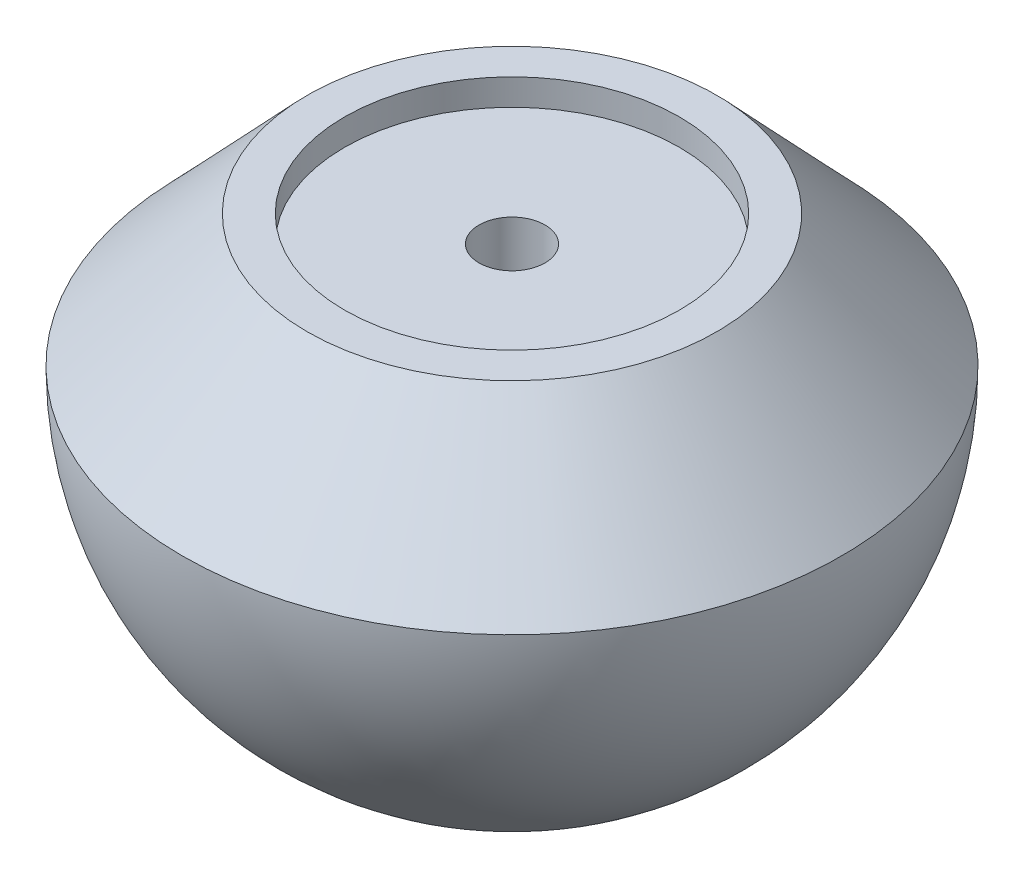
SolidWorks part; units mm, degrees
ref_plane "Front Plane" through (0, 0, 0) normal (0, 0, 1) x (1, 0, 0)
ref_plane "Top Plane" through (0, 0, 0) normal (0, 1, 0) x (1, 0, 0)
ref_plane "Right Plane" through (0, 0, 0) normal (1, 0, 0) x (0, 0, -1)
other "Configuration Table"
sketch "Sketch1" plane through (0, 0, 0) normal (0, 0, 1) x (1, 0, 0)
  line L0 (0, 0) -> (0, -25) construction
  line L1 (0, 0) -> (0, 13) construction
  line L2 (0, 13) -> (-12.7, 13) construction
  line L3 (0, 13) -> (12.7, 13) construction
  line L4 (0, 0) -> (-25, 0) construction
  line L5 (0, 0) -> (25, 0) construction
  line L6 (-15.5385, 10) -> (-25, 0)
  line L7 (15.5385, 10) -> (25, 0)
  line L8 (-12.7, 10) -> (-12.7, 8)
  line L9 (-12.7, 8) -> (-2.5, 8)
  line L10 (12.7, 8) -> (12.7, 10)
  line L11 (-2.5, 8) -> (-2.5, -12)
  line L12 (2.5, 8) -> (2.5, -12.0042)
  line L13 (-2.5, 8) -> (0, 8) construction
  line L14 (2.5, 8) -> (12.7, 8)
  line L15 (0, 8) -> (2.5, 8) construction
  line L16 (-2.5, -12) -> (-5, -12)
  line L17 (-5, -12) -> (-5, -22)
  line L18 (2.5, -12.0042) -> (5, -12.0042)
  line L19 (5, -12.0042) -> (5, -22)
  line L20 (0, 10) -> (-12.7, 10) construction
  line L21 (0, 10) -> (12.7, 10) construction
  line L22 (-12.7, 10) -> (-15.5385, 10)
  line L23 (12.7, 10) -> (15.5385, 10)
  line L24 (-12.7, 13) -> (-15.5385, 10) construction
  line L25 (-12.7, 13) -> (-12.7, 10) construction
  line L26 (12.7, 10) -> (12.7, 13) construction
  line L27 (12.7, 13) -> (15.5385, 10) construction
  line L28 (-5, -22) -> (-11.8743, -22)
  line L29 (5, -22) -> (11.8743, -22)
  line L30 (-5, -22) -> (-5, -24.4949) construction
  line L31 (5, -22) -> (5, -24.4949) construction
  line L32 (0, -22) -> (-5, -22) construction
  line L33 (0, -22) -> (5, -22) construction
  arc A0 (-25, 0) -> (-11.8743, -22) centre (0, 0) ccw
  arc A1 (0, -25) -> (5, -24.4949) centre (0, 0) ccw construction
  arc A2 (11.8743, -22) -> (25, 0) centre (0, 0) ccw
  arc A3 (-5, -24.4949) -> (0, -25) centre (0, 0) ccw construction
  arc A4 (-11.8743, -22) -> (-5, -24.4949) centre (0, 0) ccw construction
  arc A5 (5, -24.4949) -> (11.8743, -22) centre (0, 0) ccw construction
  dimension "D4" = 5
  dimension "D1" = 25
  dimension "D2" = 25.4
  dimension "D3" = 3
  dimension "D5" = 20
  dimension "D6" = 20.0042
  dimension "D7" = 2.5
  dimension "D8" = 5
  dimension "D9" = 3
  dimension "D10" = 13
revolve "Revolve1" add sketch "Sketch1" angle 360 about L0
fillet "Fillet1" radius 0.5 2 edges at (0, -22, 11.8743) (0, -22, 5)
